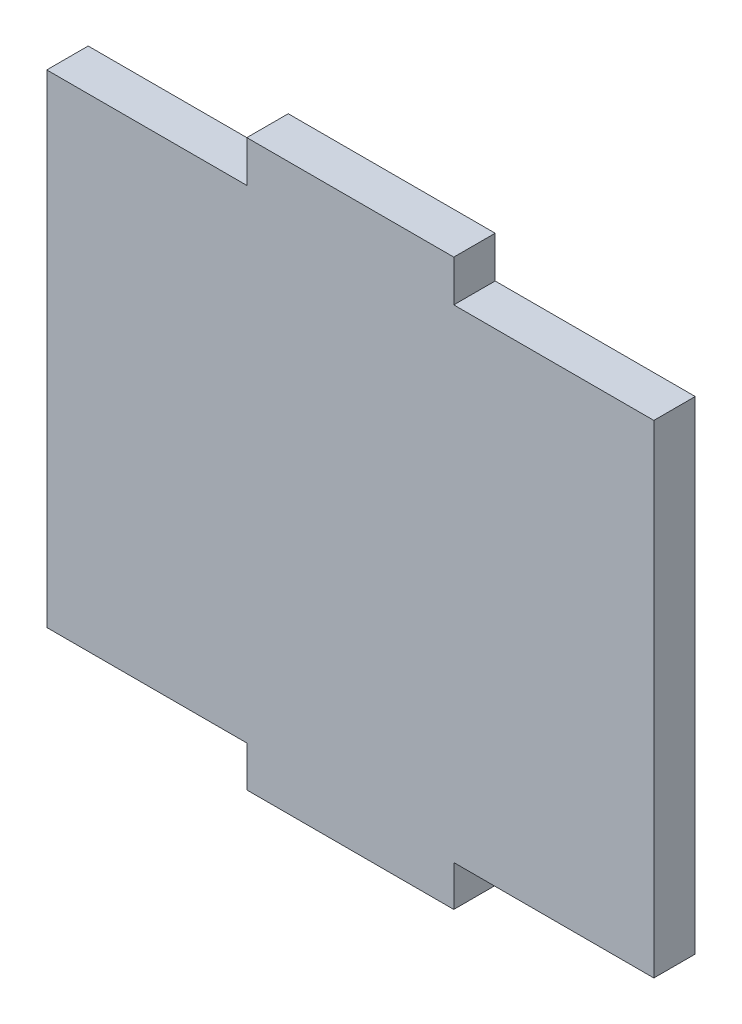
SolidWorks part; units mm, degrees
ref_plane "前视基准面" through (0, 0, 0) normal (0, 0, 1) x (1, 0, 0)
ref_plane "上视基准面" through (0, 0, 0) normal (0, 1, 0) x (1, 0, 0)
ref_plane "右视基准面" through (0, 0, 0) normal (1, 0, 0) x (0, 0, -1)
sketch "草图1" plane through (0, 0, 0) normal (0, 0, 1) x (1, 0, 0)
  line L0 (-7.5, 20.5) -> (7.5, 20.5)
  line L1 (-27.1429, 20.5) -> (27.1429, 20.5) construction
  line L2 (-7.5, -20.4474) -> (7.5, -20.4474)
  line L3 (-22, -17.5) -> (22, -17.5) construction
  line L4 (22, 17.5) -> (22, -17.5)
  line L5 (0, -17.5) -> (0, 20.5) construction
  line L6 (-22, 0) -> (22, 0) construction
  line L7 (7.5, 20.5) -> (7.5, 17.5)
  line L8 (7.5, 17.5) -> (22, 17.5)
  line L9 (7.5, -20.4474) -> (7.5, -17.5)
  line L10 (7.5, -17.5) -> (22, -17.5)
  line L11 (-7.5, -17.5) -> (-22, -17.5)
  line L12 (-7.5, -20.4474) -> (-7.5, -17.5)
  line L13 (-7.5, 17.5) -> (-22, 17.5)
  line L14 (-7.5, 20.5) -> (-7.5, 17.5)
  line L15 (-22, 17.5) -> (-22, -17.5)
  point P0 (0, 0)
  point P8 (0, 20.5)
  point P12 (0, 0)
  point P13 (0, -17.5)
  point P20 (0, -20.4474)
  dimension "D1" = 38
  dimension "D2" = 3
  dimension "D3" = 44
  dimension "D4" = 15
  dimension "D5" = 15
extrude "凸台-拉伸1" add sketch "草图1" along normal blind 3
